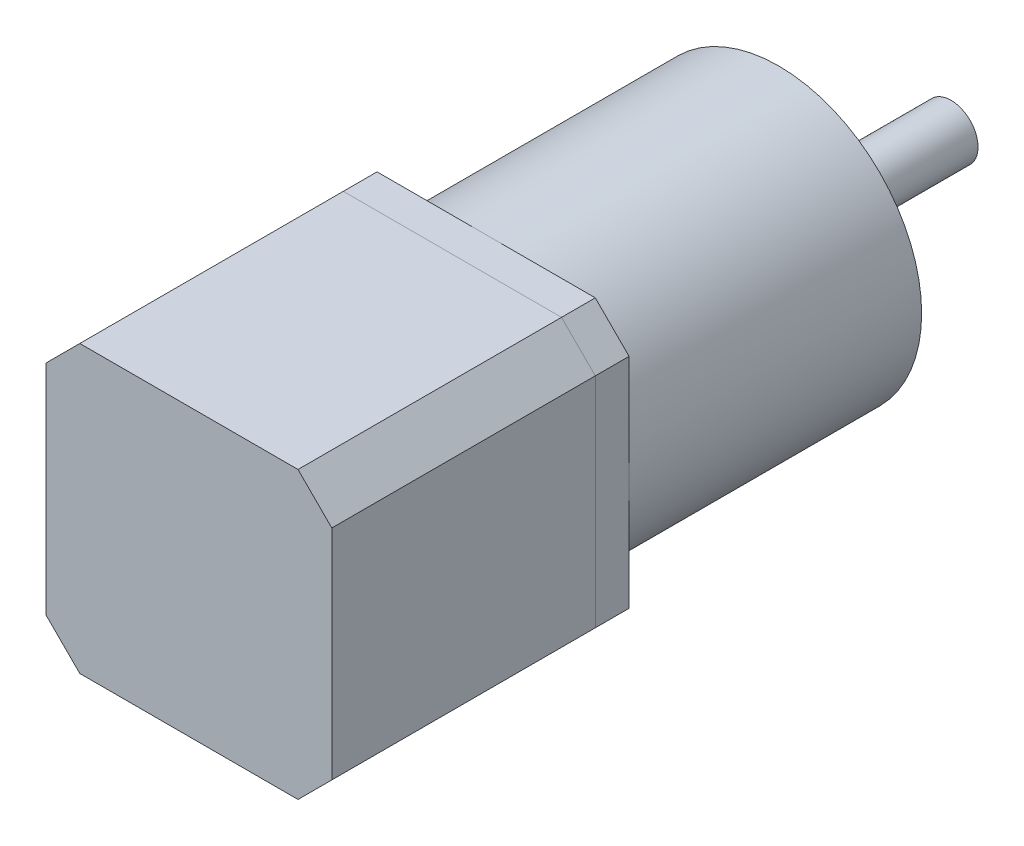
SolidWorks part; units mm, degrees
ref_plane "Front Plane" through (0, 0, 0) normal (0, 0, 1) x (1, 0, 0)
ref_plane "Top Plane" through (0, 0, 0) normal (0, 1, 0) x (1, 0, 0)
ref_plane "Right Plane" through (0, 0, 0) normal (1, 0, 0) x (0, 0, -1)
sketch "Sketch1" plane through (0, 0, 0) normal (0, 0, 1) x (1, 0, 0)
  line L1 (-21.15, 21.15) -> (21.15, 21.15)
  line L2 (-21.15, 21.15) -> (-21.15, -21.15)
  line L3 (-21.15, -21.15) -> (21.15, -21.15)
  line L4 (21.15, 21.15) -> (21.15, -21.15)
  line L5 (-21.15, 21.15) -> (21.15, -21.15) construction
  line L6 (-21.15, -21.15) -> (21.15, 21.15) construction
  point P0 (0, 0)
  dimension "D1" = 42.3
  dimension "D2" = 42.3
extrude "Boss-Extrude1" add sketch "Sketch1" along normal blind 39
chamfer "Chamfer1" distance 5 angle 45 4 edges at (-21.15, -21.15, 19.5) (21.15, -21.15, 19.5) (-21.15, 21.15, 19.5) (21.15, 21.15, 19.5)
sketch "Sketch2" plane through (0, 0, 0) normal (0, 0, -1) x (-1, 0, 0)
  line L1 (-21.15, -21.15) -> (21.15, -21.15)
  line L2 (-21.15, -21.15) -> (-21.15, 21.15)
  line L3 (-21.15, 21.15) -> (21.15, 21.15)
  line L4 (21.15, -21.15) -> (21.15, 21.15)
  line L5 (-21.15, -21.15) -> (21.15, 21.15) construction
  line L6 (-21.15, 21.15) -> (21.15, -21.15) construction
  point P0 (0, 0)
  dimension "D1" = 42.3
  dimension "D2" = 42.3
extrude "Boss-Extrude2" add sketch "Sketch2" along normal blind 5 separate body
chamfer "Chamfer2" distance 5 angle 45 4 edges at (21.15, -21.15, -2.5) (-21.15, -21.15, -2.5) (21.15, 21.15, -2.5) (-21.15, 21.15, -2.5)
sketch "Sketch3" plane through (0, 0, -5) normal (0, 0, -1) x (-1, 0, 0)
  circle A0 centre (0, 0) radius 21.15
  dimension "D1" = 42.3
extrude "Boss-Extrude3" add sketch "Sketch3" along normal blind 43.3
sketch "Sketch4" plane through (0, 0, -48.3) normal (0, 0, -1) x (-1, 0, 0)
  circle A0 centre (0, 0) radius 11
  dimension "D1" = 22
extrude "Boss-Extrude4" add sketch "Sketch4" along normal blind 2
sketch "Sketch5" plane through (0, 0, -50.3) normal (0, 0, -1) x (-1, 0, 0)
  circle A0 centre (0, 0) radius 4
  dimension "D1" = 8
extrude "Boss-Extrude5" add sketch "Sketch5" along normal blind 23.5
sketch "Sketch6" plane through (0, 0, -50.3) normal (0, 0, -1) x (-1, 0, 0)
  circle A0 centre (0, 0) radius 6.211
extrude "Boss-Extrude6" add sketch "Sketch6" along normal blind 0.5
sketch "Sketch7" plane through (0, 0, -48.3) normal (0, 0, -1) x (-1, 0, 0)
  circle A0 centre (0, 0) radius 17.5 construction
  circle A1 centre (0, 17.5) radius 1.1442
  circle A2 centre (17.5, 0) radius 1.1442
  circle A3 centre (0, -17.5) radius 1.1442
  circle A4 centre (-17.5, 0) radius 1.1442
  point P16 (0, 0)
  dimension "D1" = 35
  dimension "D2" = 4
extrude "Cut-Extrude1" cut sketch "Sketch7" against normal blind 10
